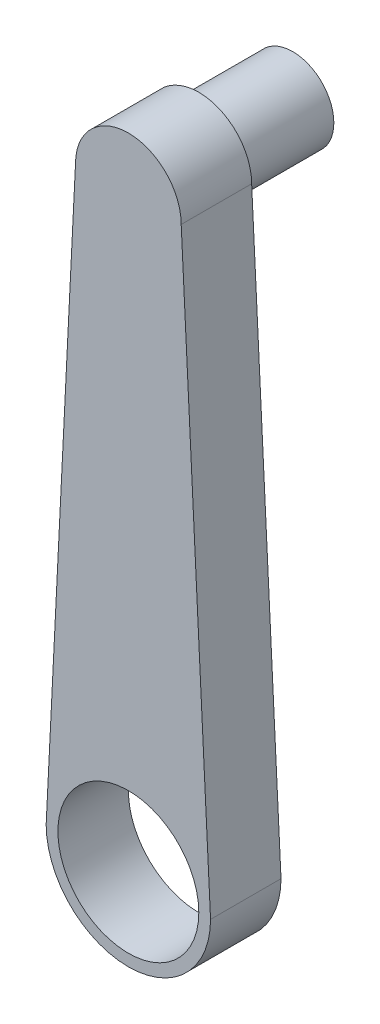
SolidWorks part; units mm, degrees
ref_plane "Спереди" through (0, 0, 0) normal (0, 0, 1) x (1, 0, 0)
ref_plane "Сверху" through (0, 0, 0) normal (0, 1, 0) x (1, 0, 0)
ref_plane "Справа" through (0, 0, 0) normal (1, 0, 0) x (0, 0, -1)
sketch "Эскиз1" plane through (0, 0, 0) normal (0, 0, 1) x (1, 0, 0)
  line L0 (-70, 0) -> (-45, 500)
  line L1 (45, 500) -> (70, 0)
  arc A0 (-69.6509, 6.9825) -> (69.6509, 6.9825) centre (0, 0) ccw
  arc A1 (45, 500) -> (-45, 500) centre (0, 500) ccw
  dimension "D1" = 140
  dimension "D3" = 90
  dimension "D2" = 500
extrude "Бобышка-Вытянуть1" add sketch "Эскиз1" along normal blind 60 contours L1 A1 L0 A0
sketch "Эскиз2" plane through (0, 0, 60) normal (0, 0, 1) x (1, 0, 0)
  circle A0 centre (0, 0) radius 60
  dimension "D1" = 120
extrude "Вырез-Вытянуть1" cut sketch "Эскиз2" against normal blind 60 contours A0
sketch "Эскиз3" plane through (0, 0, 0) normal (0, 0, -1) x (-1, 0, 0)
  circle A0 centre (0, 500) radius 35
  dimension "D2" = 70
  dimension "D1" = 500
extrude "Бобышка-Вытянуть2" add sketch "Эскиз3" along normal blind 80
